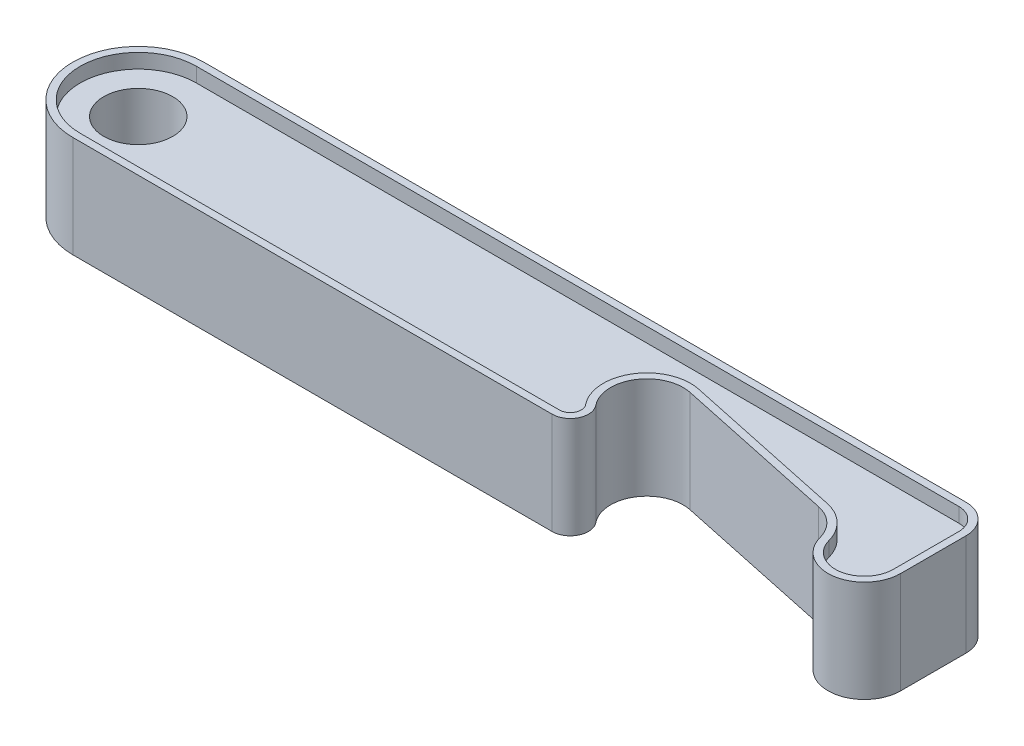
SolidWorks part; units mm, degrees
material "AISI 1020"
ref_plane "Front Plane" through (0, 0, 0) normal (0, 0, 1) x (1, 0, 0)
ref_plane "Top Plane" through (0, 0, 0) normal (0, 1, 0) x (1, 0, 0)
ref_plane "Right Plane" through (0, 0, 0) normal (1, 0, 0) x (0, 0, -1)
sketch "Sketch1" plane through (0, 0, 0) normal (0, 1, 0) x (1, 0, 0)
  line L4 (0, 9) -> (105, 9)
  line L5 (109, 5) -> (109, -4)
  line L6 (95.3761, -1.6817) -> (72.8761, 3.1008)
  line L7 (66, -9) -> (0, -9)
  circle A9 centre (0, 0) radius 4.75
  arc A10 (105, 9) -> (109, 5) centre (105, 5) cw
  arc A11 (109, -4) -> (99.1683, -5.2862) centre (104, -4) cw
  arc A12 (99.1683, -5.2862) -> (95.3761, -1.6817) centre (94.3365, -6.5724) ccw
  arc A13 (72.8761, 3.1008) -> (67.9455, -4.93) centre (71.8365, -1.7899) ccw
  arc A14 (67.9455, -4.93) -> (66, -9) centre (66, -6.5) cw
  arc A15 (0, -9) -> (0, 9) centre (0, 0) cw
  point P20 (0, 0)
  point P21 (72, -2.8619)
  point P22 (79.1186, 2.481)
  point P23 (52.0472, -4.6369)
  point P24 (55.5607, 5)
  point P25 (78.1205, -0.4873)
  point P26 (0, 0)
  dimension "D1" = 9.5
  dimension "D3" = 4
  dimension "D4" = 5
  dimension "D5" = 2.5
  dimension "D2" = 18
  dimension "D6" = 22.5
  dimension "D7" = 12
  dimension "D8" = 109
  dimension "D9" = 13
  dimension "D10" = 9
  dimension "D11" = 38
extrude "Boss-Extrude1" add sketch "Sketch1" along normal blind 14
sketch "Sketch4" plane through (0, 14, 0) normal (0, 1, 0) x (1, 0, 0)
  line L8 (0, -8) -> (66, -8)
  line L9 (73.084, 4.079) -> (95.584, -0.7036)
  line L10 (108, -4) -> (108, 5)
  line L11 (105, 8) -> (0, 8)
  line L12 (0, -8) -> (66, -8)
  line L13 (73.084, 4.079) -> (95.584, -0.7036)
  line L14 (108, -4) -> (108, 5)
  line L15 (105, 8) -> (0, 8)
  arc A12 (0, 8) -> (0, -8) centre (0, 0) ccw
  arc A13 (66, -8) -> (67.1673, -5.558) centre (66, -6.5) ccw
  arc A14 (73.084, 4.079) -> (67.1673, -5.558) centre (71.8365, -1.7899) ccw
  arc A15 (100.1346, -5.029) -> (95.584, -0.7036) centre (94.3365, -6.5724) ccw
  arc A16 (100.1346, -5.029) -> (108, -4) centre (104, -4) ccw
  arc A17 (108, 5) -> (105, 8) centre (105, 5) ccw
  arc A18 (0, 8) -> (0, -8) centre (0, 0) ccw
  arc A19 (66, -8) -> (67.1673, -5.558) centre (66, -6.5) ccw
  arc A20 (73.084, 4.079) -> (67.1673, -5.558) centre (71.8365, -1.7899) ccw
  arc A21 (100.1346, -5.029) -> (95.584, -0.7036) centre (94.3365, -6.5724) ccw
  arc A22 (100.1346, -5.029) -> (108, -4) centre (104, -4) ccw
  arc A23 (108, 5) -> (105, 8) centre (105, 5) ccw
  dimension "D1" = 1
extrude "Cut-Extrude1" cut sketch "Sketch4" against normal blind 2
sketch "Sketch5" plane through (0, 0, 0) normal (0, -1, 0) x (1, 0, 0)
  line L8 (0, -8) -> (105, -8)
  line L9 (108, -5) -> (108, 4)
  line L10 (95.584, 0.7036) -> (73.084, -4.079)
  line L11 (66, 8) -> (0, 8)
  line L12 (0, -8) -> (105, -8)
  line L13 (108, -5) -> (108, 4)
  line L14 (95.584, 0.7036) -> (73.084, -4.079)
  line L15 (66, 8) -> (0, 8)
  arc A12 (0, 8) -> (0, -8) centre (0, 0) ccw
  arc A13 (105, -8) -> (108, -5) centre (105, -5) ccw
  arc A14 (108, 4) -> (100.1346, 5.029) centre (104, 4) ccw
  arc A15 (95.584, 0.7036) -> (100.1346, 5.029) centre (94.3365, 6.5724) ccw
  arc A16 (67.1673, 5.558) -> (73.084, -4.079) centre (71.8365, 1.7899) ccw
  arc A17 (67.1673, 5.558) -> (66, 8) centre (66, 6.5) ccw
  arc A18 (0, 8) -> (0, -8) centre (0, 0) ccw
  arc A19 (105, -8) -> (108, -5) centre (105, -5) ccw
  arc A20 (108, 4) -> (100.1346, 5.029) centre (104, 4) ccw
  arc A21 (95.584, 0.7036) -> (100.1346, 5.029) centre (94.3365, 6.5724) ccw
  arc A22 (67.1673, 5.558) -> (73.084, -4.079) centre (71.8365, 1.7899) ccw
  arc A23 (67.1673, 5.558) -> (66, 8) centre (66, 6.5) ccw
  dimension "D1" = 1
extrude "Cut-Extrude2" cut sketch "Sketch5" against normal blind 2
equation "\"A\" = 118"
equation "\"B\" = 14"
equation "\"C\" = 2"
equation "\"D8@Sketch1\"=\"A\"-9"
equation "\"D1@Boss-Extrude1\"=\"B\""
equation "\"D1@Cut-Extrude1\"=\"C\""
equation "\"D1@Cut-Extrude2\"=\"C\""
